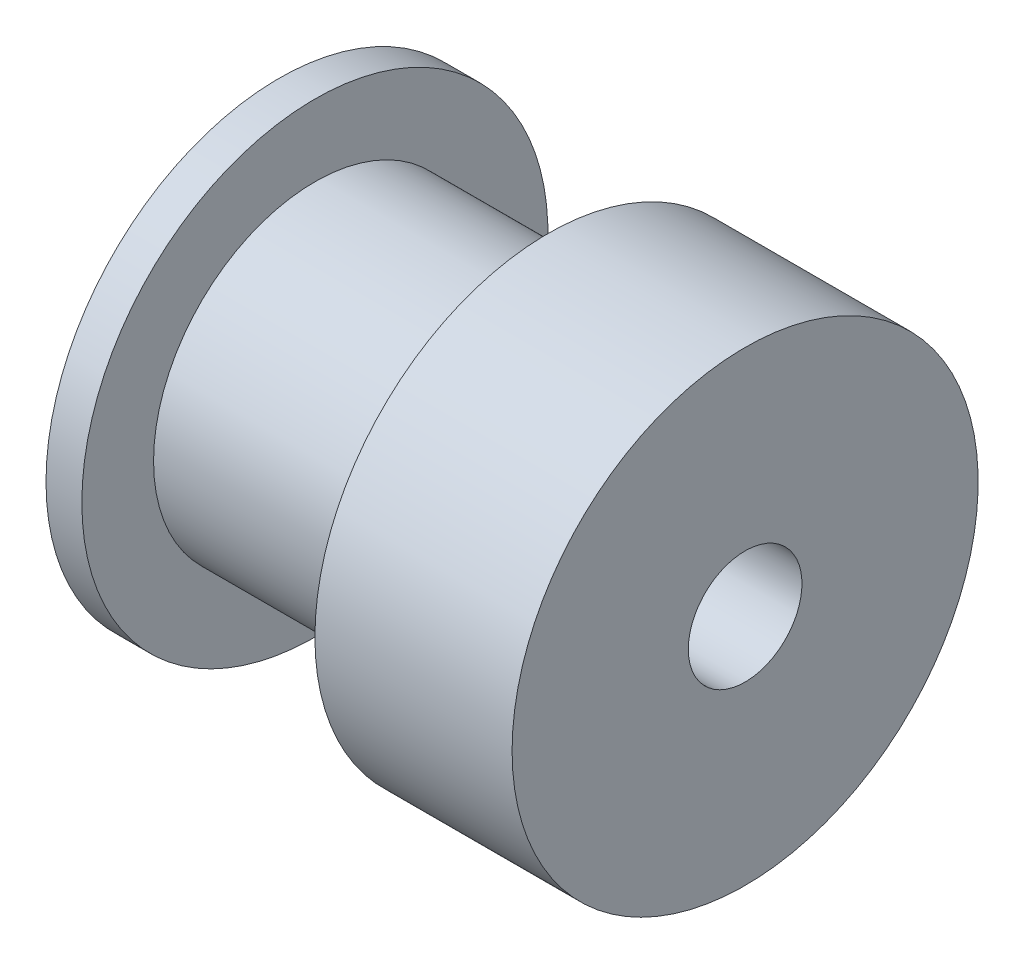
SolidWorks part; units mm, degrees
ref_plane "前视基准面" through (0, 0, 0) normal (0, 0, 1) x (1, 0, 0)
ref_plane "上视基准面" through (0, 0, 0) normal (0, 1, 0) x (1, 0, 0)
ref_plane "右视基准面" through (0, 0, 0) normal (1, 0, 0) x (0, 0, -1)
other "Configuration Table"
sketch "草图1" plane through (0, 0, 0) normal (0, 0, 1) x (1, 0, 0)
  line L0 (6.5, -3.25) -> (-6.5, -3.25)
  line L2 (-6.5, 3.25) -> (-6.5, -3.25)
  line L3 (-6.5, -3.25) -> (6.5, -3.25) construction
  line L4 (6.5, 3.25) -> (6.5, -3.25)
  line L5 (-6.5, 3.25) -> (6.5, -3.25) construction
  line L6 (-6.5, -3.25) -> (6.5, 3.25) construction
  line L7 (-6.5, 3.25) -> (-5.5, 3.25)
  line L8 (-5.5, 3.25) -> (-5.5, 1.25)
  line L9 (-5.5, 1.25) -> (1, 1.25)
  line L10 (1, 1.25) -> (1, 3.25)
  line L11 (1, 3.25) -> (6.5, 3.25)
  point P0 (0, 0)
  dimension "D1" = 13
  dimension "D2" = 6.5
  dimension "D3" = 5.5
  dimension "D4" = 1
  dimension "D5" = 2
  dimension "D6" = 2
revolve "旋转1" add sketch "草图1" angle 360 about L3
sketch "草图2" plane through (-6.5, 0, 0) normal (-1, 0, 0) x (0, 0, 1)
  line L0 (0, 3.25) -> (0, -9.75) construction
  line L1 (-6.5, -3.25) -> (6.5, -3.25) construction
  circle A0 centre (0, -3.25) radius 6.5 construction
  circle A1 centre (0, -3.25) radius 1.585
  point P7 (0, -3.25)
  dimension "D1" = 3.17
extrude "切除-拉伸1" cut sketch "草图2" against normal through all
